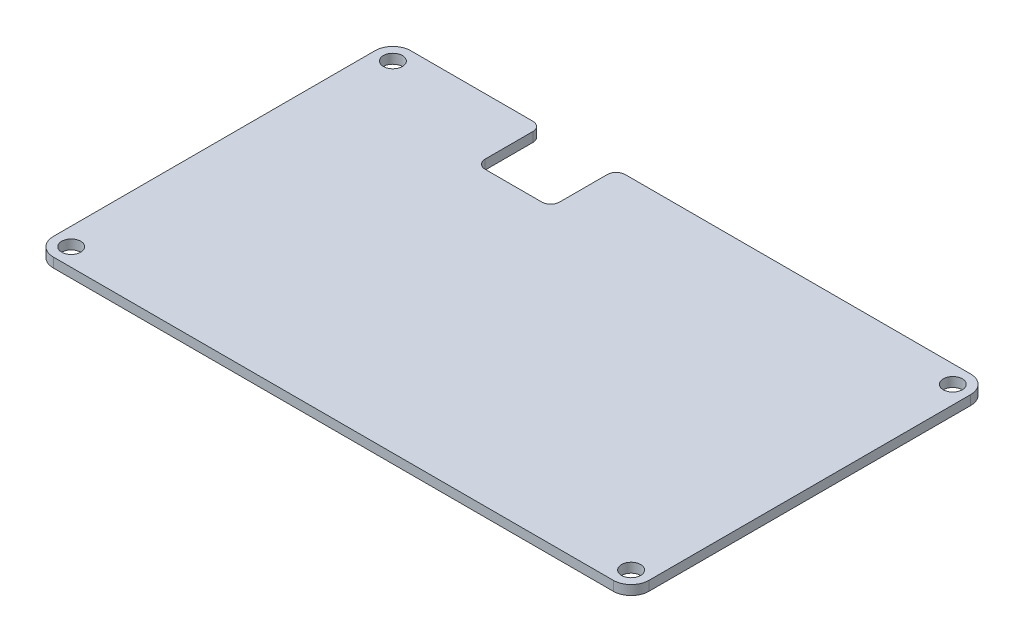
SolidWorks part; units mm, degrees
ref_plane "前视基准面" through (0, 0, 0) normal (0, 0, 1) x (1, 0, 0)
ref_plane "上视基准面" through (0, 0, 0) normal (0, 1, 0) x (1, 0, 0)
ref_plane "右视基准面" through (0, 0, 0) normal (1, 0, 0) x (0, 0, -1)
sketch "草图1" plane through (0, 0, 0) normal (0, 1, 0) x (1, 0, 0)
  line L1 (-50, 30) -> (50, 30)
  line L2 (-50, 30) -> (-50, -30)
  line L3 (-50, -30) -> (50, -30)
  line L4 (50, 30) -> (50, -30)
  line L5 (-50, 30) -> (50, -30) construction
  line L6 (-50, -30) -> (50, 30) construction
  point P0 (0, 0)
  dimension "D1" = 100
  dimension "D2" = 60
extrude "凸台-拉伸1" add sketch "草图1" along normal blind 1.6
sketch "草图2" plane through (0, 1.6, 0) normal (0, 1, 0) x (1, 0, 0)
  line L0 (0, 11.4648) -> (0, -11.1115) construction
  line L1 (-16.7682, 0) -> (14.1439, 0) construction
  line L2 (-50, 30) -> (50, 30) construction
  line L3 (-50, 30) -> (-50, -30) construction
  circle A0 centre (-47, 27) radius 1.6
  circle A1 centre (47, 27) radius 1.6
  circle A2 centre (47, -27) radius 1.6
  circle A3 centre (-47, -27) radius 1.6
  dimension "D1" = 3.2
  dimension "D2" = 3
  dimension "D3" = 3
extrude "切除-拉伸1" cut sketch "草图2" against normal through all
sketch "草图3" plane through (0, 1.6, 0) normal (0, 1, 0) x (1, 0, 0)
  line L0 (-50, 30) -> (50, 30) construction
  line L1 (-25, 30) -> (-12.5, 30)
  line L2 (-25, 30) -> (-25, 19)
  line L3 (-25, 19) -> (-12.5, 19)
  line L4 (-12.5, 30) -> (-12.5, 19)
  line L6 (-50, 30) -> (-50, -30) construction
  dimension "D1" = 12.5
  dimension "D2" = 11
  dimension "D3" = 25
extrude "切除-拉伸2" cut sketch "草图3" against normal through all
fillet "圆角1" radius 3 4 edges at (50, 0.8, -30) (50, 0.8, 30) (-50, 0.8, 30) (-50, 0.8, -30)
fillet "圆角2" radius 1.5 4 edges at (-12.5, 0.8, -30) (-25, 0.8, -30) (-12.5, 0.8, -19) (-25, 0.8, -19)
